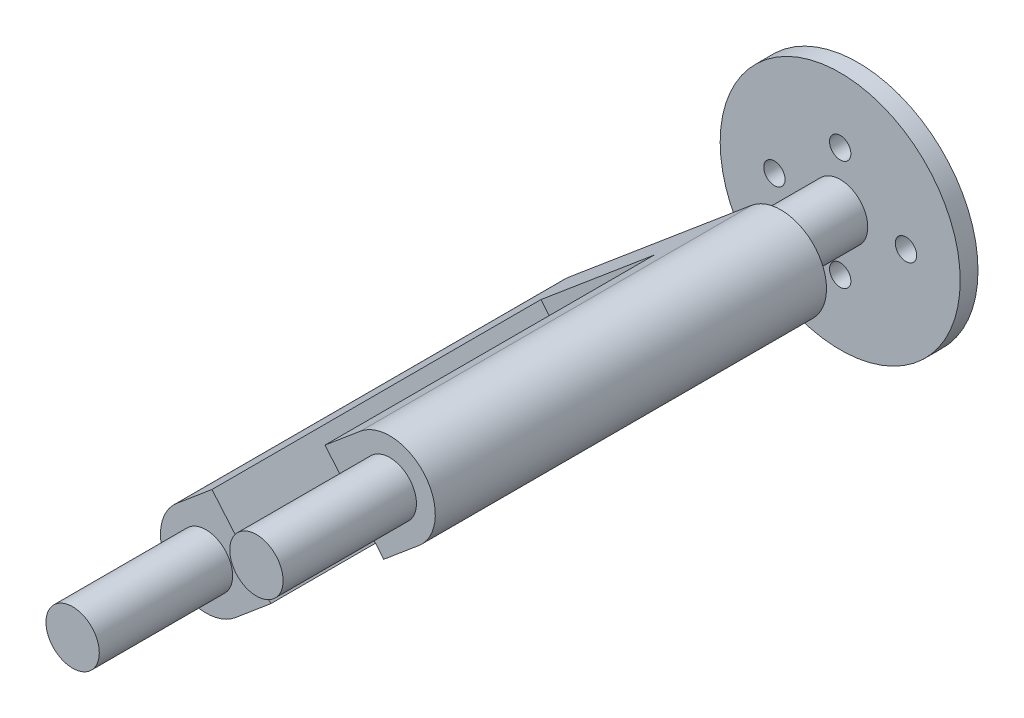
SolidWorks part; units mm, degrees
ref_plane "Front" through (0, 0, 0) normal (0, 0, 1) x (1, 0, 0)
ref_plane "Top" through (0, 0, 0) normal (0, 1, 0) x (1, 0, 0)
ref_plane "Right" through (0, 0, 0) normal (1, 0, 0) x (0, 0, -1)
sketch "Sketch1" plane through (0, 0, 0) normal (0, 0, 1) x (1, 0, 0)
  line L0 (0, 0) -> (-9.398, 0) construction
  circle A0 centre (0, 0) radius 17.145
  circle A1 centre (0, 0) radius 3.937
  circle A2 centre (0, 7.874) radius 1.524
  circle A4 centre (0, -7.874) radius 1.524
  circle A6 centre (7.874, 0) radius 1.524 [skipped]
  circle A7 centre (-7.874, 0) radius 1.524 [skipped]
  circle A8 centre (-9.398, 0) radius 1.524
  circle A9 centre (9.398, 0) radius 1.524
  point P15 (0, 0)
  dimension "D1" = 34.29
  dimension "D2" = 7.874
  dimension "D4" = 3.048
  dimension "D7" = 3.048
  dimension "D3" = 7.874
  dimension "D6" = 9.398
  dimension "D5" = 4
  dimension "D8" = 2
extrude "Boss-Extrude1" add sketch "Sketch1" along normal blind 2.54
sketch "Sketch2" plane through (0, 0, 2.54) normal (0, 0, 1) x (1, 0, 0)
  circle A0 centre (0, 0) radius 3.937
extrude "Boss-Extrude2" add sketch "Sketch2" along normal blind 73.66 and the other way blind 2.54
sketch "Sketch8" plane through (0, 0, 2.54) normal (0, 0, 1) x (1, 0, 0)
  line L0 (-3.0065, -2.5418) -> (-13.0928, -11.0693)
  circle A0 centre (0, 0) radius 3.937 construction
  circle A1 centre (0, 0) radius 17.145 construction
sketch "Sketch9" plane through (0, 0, 76.2) normal (0, 0, 1) x (1, 0, 0)
  line L0 (13.1267, 11.0291) -> (-13.1267, -11.0291) construction
  line L1 (17.3103, 6.0498) -> (-8.9431, -16.0084)
  line L2 (8.9431, 16.0084) -> (-17.3103, -6.0498)
  arc A0 (17.3103, 6.0498) -> (8.9431, 16.0084) centre (13.1267, 11.0291) ccw
  arc A1 (-17.3103, -6.0498) -> (-8.9431, -16.0084) centre (-13.1267, -11.0291) ccw
  point P2 (0, 0)
  dimension "D1" = 34.29
extrude "Boss-Extrude8" add sketch "Sketch9" along normal blind 3.81 and the other way blind 52.07
sketch "Sketch10" plane through (0, 0, 80.01) normal (0, 0, 1) x (1, 0, 0)
  line L0 (4.1836, -4.9793) -> (1.8594, -2.213)
  line L1 (-8.9431, -16.0084) -> (17.3103, 6.0498) construction
  circle A0 centre (-13.1267, -11.0291) radius 3.81
  circle A1 centre (13.1267, 11.0291) radius 3.81
  dimension "D1" = 7.62
extrude "Boss-Extrude9" add sketch "Sketch10" along normal blind 19.05 contours A1 | A0
sketch "Sketch11" plane through (0, 0, 80.01) normal (0, 0, 1) x (1, 0, 0)
  line L0 (3.374, 12.3359) -> (-12.7252, -1.2753)
  line L1 (3.374, 12.3359) -> (12.7252, 1.2753)
  line L2 (-12.7252, -1.2753) -> (-3.374, -12.3359)
  line L3 (12.7252, 1.2753) -> (-3.374, -12.3359)
  line L4 (3.374, 12.3359) -> (-3.374, -12.3359) construction
  line L5 (-12.7252, -1.2753) -> (12.7252, 1.2753) construction
  point P1 (0, 0)
extrude "Cut-Extrude1" cut sketch "Sketch11" against normal blind 46.99
fillet "Fillet3" radius 2.54 1 edges at (3.937, 0, 24.13)
